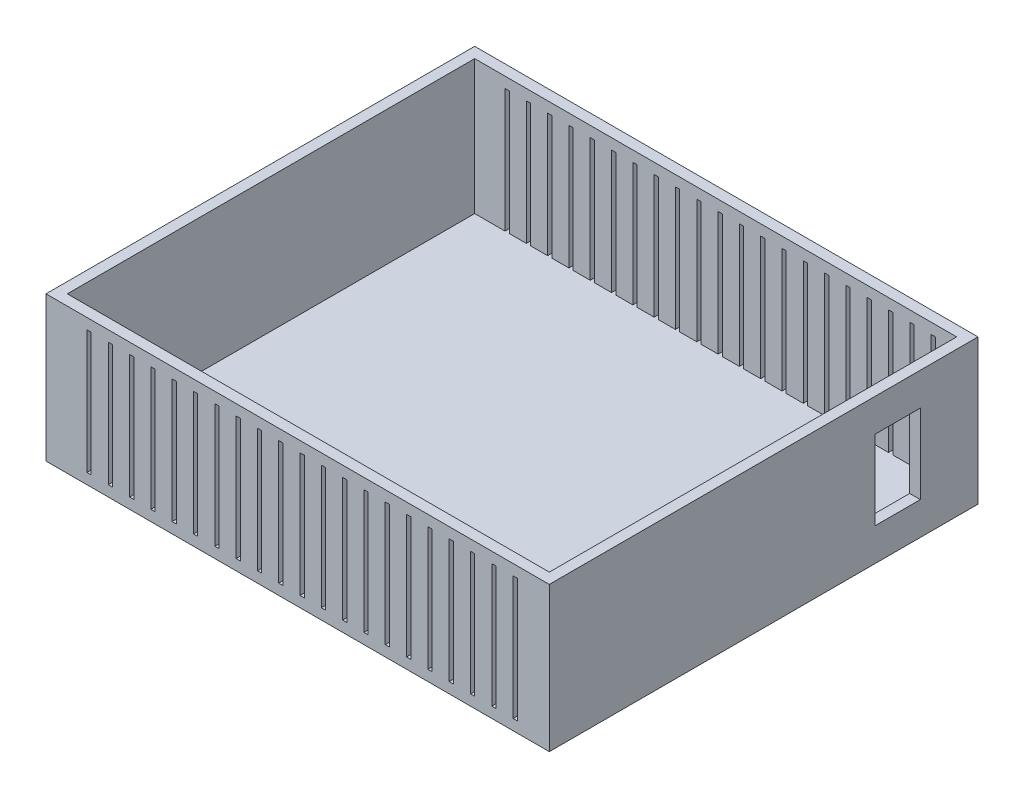
SolidWorks part; units mm, degrees
ref_plane "Front Plane" through (0, 0, 0) normal (0, 0, 1) x (1, 0, 0)
ref_plane "Top Plane" through (0, 0, 0) normal (0, 1, 0) x (1, 0, 0)
ref_plane "Right Plane" through (0, 0, 0) normal (1, 0, 0) x (0, 0, -1)
sketch "Sketch1" plane through (0, 0, 0) normal (0, 1, 0) x (1, 0, 0)
  line L0 (-143.65, -121.412) -> (-143.65, 121.412)
  line L1 (150, -127.762) -> (-150, -127.762)
  line L2 (150, -127.762) -> (150, 127.762)
  line L3 (150, 127.762) -> (-150, 127.762)
  line L4 (-150, -127.762) -> (-150, 127.762)
  line L5 (150, -127.762) -> (-150, 127.762) construction
  line L6 (150, 127.762) -> (-150, -127.762) construction
  line L7 (143.65, 121.412) -> (-143.65, 121.412)
  line L8 (143.65, -121.412) -> (143.65, 121.412)
  line L9 (143.65, -121.412) -> (-143.65, -121.412)
  point P0 (0, 0)
  dimension "D1" = 300
  dimension "D2" = 6.35
  dimension "D3" = 255.524
extrude "Boss-Extrude1" add sketch "Sketch1" along normal blind 80
sketch "Sketch2" plane through (0, 0, 0) normal (0, -1, 0) x (1, 0, 0)
  line L0 (150, -127.762) -> (-150, -127.762) construction
  line L1 (150, 127.762) -> (150, -127.762) construction
  line L2 (-150, 127.762) -> (150, 127.762) construction
  line L3 (-150, -127.762) -> (-150, 127.762) construction
  line L4 (150, -127.762) -> (-150, -127.762)
  line L5 (150, 127.762) -> (150, -127.762)
  line L6 (-150, 127.762) -> (150, 127.762)
  line L7 (-150, -127.762) -> (-150, 127.762)
extrude "Boss-Extrude2" add sketch "Sketch2" along normal blind 6.35
sketch "Sketch4" plane through (150, 0, 0) normal (1, 0, 0) x (0, 0, -1)
  line L0 (127.762, 80) -> (127.762, -6.35) construction
  line L1 (93.3932, 60.45) -> (66.3632, 60.45)
  line L2 (93.3932, 60.45) -> (93.3932, 13.2)
  line L3 (93.3932, 13.2) -> (66.3632, 13.2)
  line L4 (66.3632, 60.45) -> (66.3632, 13.2)
  line L5 (93.3932, 60.45) -> (66.3632, 13.2) construction
  line L6 (93.3932, 13.2) -> (66.3632, 60.45) construction
  point P0 (79.8782, 36.825)
  point P8 (127.762, 36.825)
  dimension "D1" = 47.25
  dimension "D2" = 27.03
extrude "Cut-Extrude1" cut sketch "Sketch4" against normal up to surface (6.35 mm away) up to face at (143.65, 40, 0)
sketch "Sketch5" plane through (0, 0, -127.762) normal (0, 0, -1) x (-1, 0, 0)
  line L0 (-143.65, 73.65) -> (143.65, 73.65)
  line L1 (-130.95, 73.65) -> (-130.95, 0)
  line L2 (-128.41, 73.65) -> (-128.41, 0)
  line L4 (-143.65, 0) -> (143.65, 0)
  line L5 (143.65, 0) -> (143.65, 80)
  line L6 (143.65, 80) -> (-143.65, 80)
  line L7 (-143.65, 80) -> (-143.65, 0)
  line L8 (-143.65, 0) -> (143.65, 0)
  line L9 (143.65, 0) -> (143.65, 80)
  line L10 (143.65, 80) -> (-143.65, 80)
  line L11 (-143.65, 80) -> (-143.65, 0)
  dimension "D2" = 6.35
  dimension "D3" = 2.54
  dimension "D4" = 12.7
  dimension "D1" = 0
extrude "Boss-Extrude4" add sketch "Sketch5" against normal blind 324.866 separate body contours L1 L8 L2 L0
pattern_linear "LPattern2" count 21 spacing 12.7 along (-1, 0, 0) of "Boss-Extrude4"
combine bodies "Combine2" operation type subtract main body 104 bodies to subtract 206 105 196 197 199 198 200 201 202 203 205 204 207 208 210 211 214 215 213 212 209
